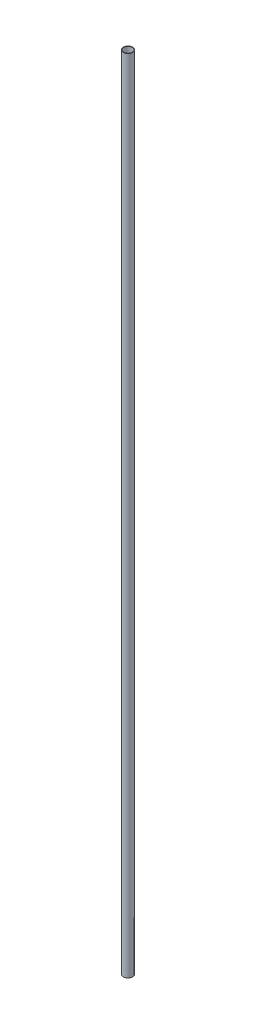
SolidWorks part; units mm, degrees
material "Thornel Mat VMA"
ref_plane "Front Plane" through (0, 0, 0) normal (0, 0, 1) x (1, 0, 0)
ref_plane "Top Plane" through (0, 0, 0) normal (0, 1, 0) x (1, 0, 0)
ref_plane "Right Plane" through (0, 0, 0) normal (1, 0, 0) x (0, 0, -1)
sketch "Sketch1" plane through (0, 0, 0) normal (0, 1, 0) x (1, 0, 0)
  circle A0 centre (0, 0) radius 10.541
  circle A1 centre (0, 0) radius 9.525
  dimension "D1" = 1.016
  dimension "D2" = 19.05
extrude "Boss-Extrude1" add sketch "Sketch1" along normal blind 1803.4
sketch3d "3DSketch1" plane through (0, 0, 0) normal (0, 0, 1) x (1, 0, 0)
  dimension "D1" = 355.6
